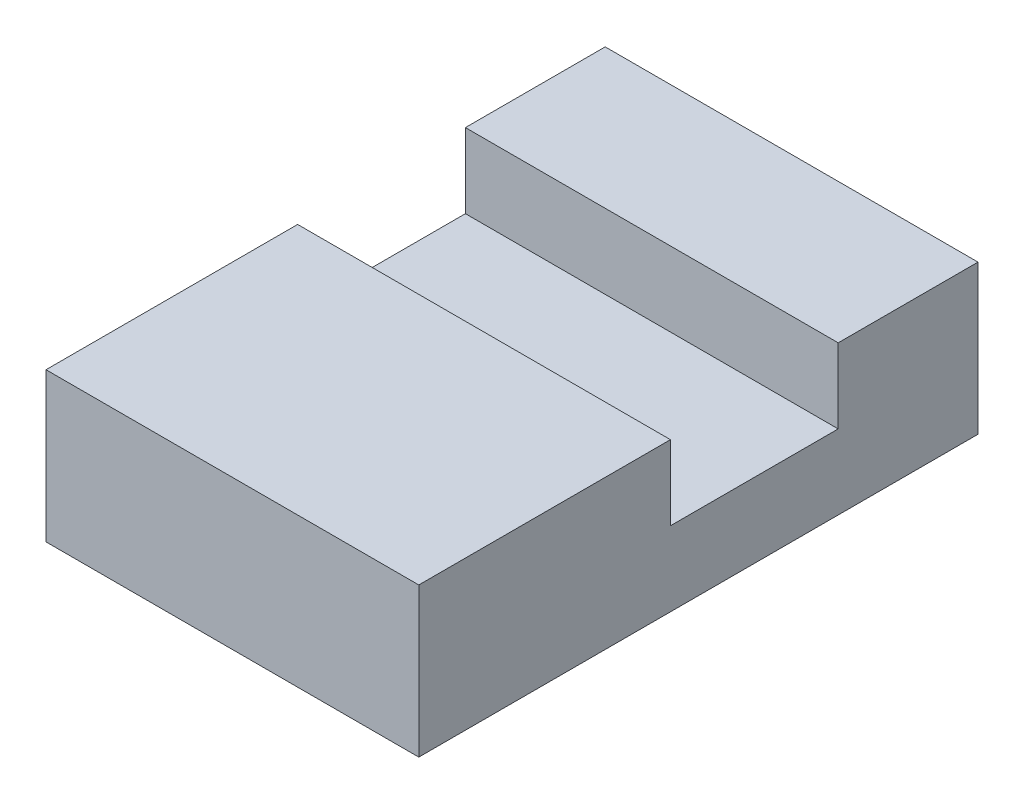
SolidWorks part; units mm, degrees
ref_plane "Front Plane" through (0, 0, 0) normal (0, 0, 1) x (1, 0, 0)
ref_plane "Top Plane" through (0, 0, 0) normal (0, 1, 0) x (1, 0, 0)
ref_plane "Right Plane" through (0, 0, 0) normal (1, 0, 0) x (0, 0, -1)
sketch "Sketch1" plane through (0, 0, 0) normal (0, 1, 0) x (1, 0, 0)
  line L1 (-14.1818, 9.5909) -> (5.8182, 9.5909)
  line L2 (-14.1818, 9.5909) -> (-14.1818, -20.4091)
  line L3 (-14.1818, -20.4091) -> (5.8182, -20.4091)
  line L4 (5.8182, 9.5909) -> (5.8182, -20.4091)
  dimension "D1" = 20
  dimension "D2" = 30
extrude "Boss-Extrude1" add sketch "Sketch1" along normal blind 8
sketch "Sketch3" plane through (5.8182, 0, 0) normal (1, 0, 0) x (0, 0, -1)
  line L0 (-20.4091, 8) -> (9.5909, 8) construction
  line L1 (2.0909, 8) -> (-6.9091, 8)
  line L2 (2.0909, 8) -> (2.0909, 4)
  line L3 (2.0909, 4) -> (-6.9091, 4)
  line L4 (-6.9091, 8) -> (-6.9091, 4)
  line L5 (9.5909, 8) -> (9.5909, 0) construction
  dimension "D1" = 4
  dimension "D2" = 9
  dimension "D3" = 7.5
extrude "Cut-Extrude1" cut sketch "Sketch3" against normal blind 20
